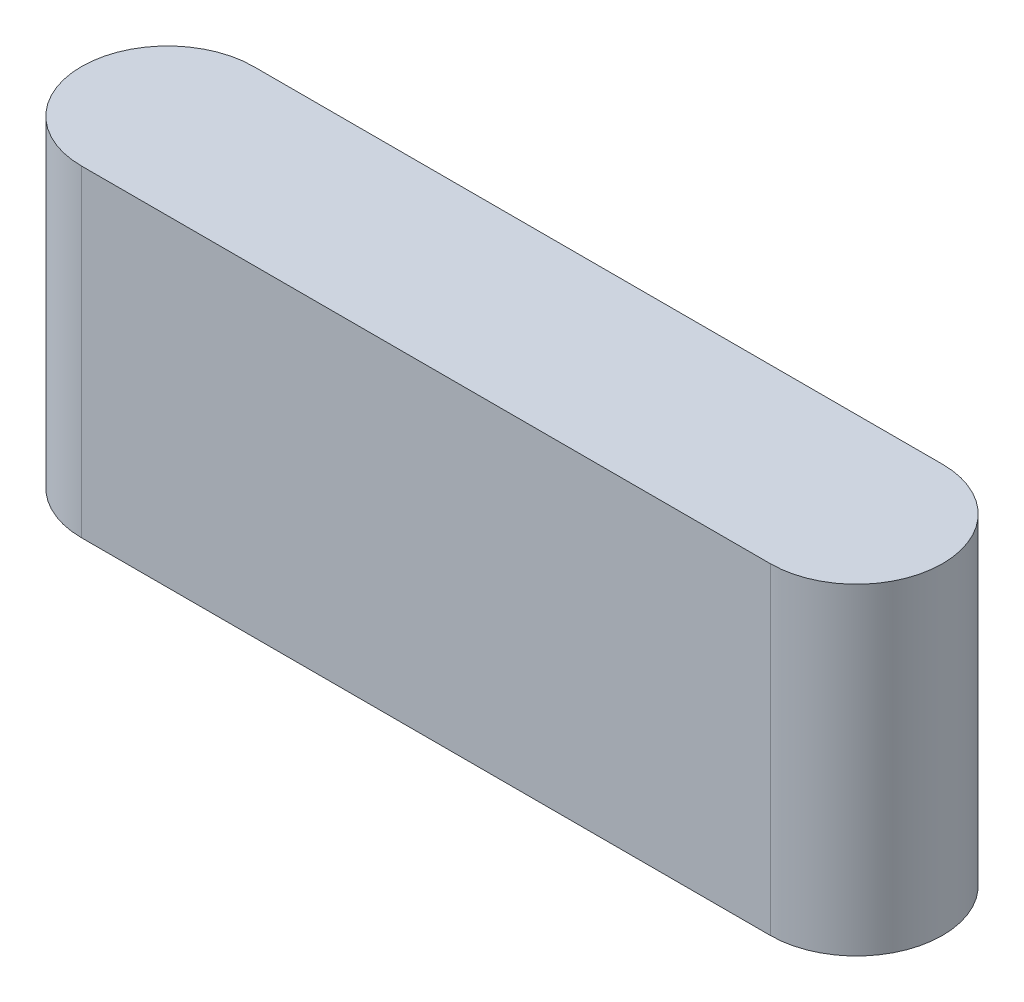
SolidWorks part; units mm, degrees
ref_plane "Front Plane" through (0, 0, 0) normal (0, 0, 1) x (1, 0, 0)
ref_plane "Top Plane" through (0, 0, 0) normal (0, 1, 0) x (1, 0, 0)
ref_plane "Right Plane" through (0, 0, 0) normal (1, 0, 0) x (0, 0, -1)
sketch "Sketch1" plane through (0, 0, 0) normal (0, 1, 0) x (1, 0, 0)
  line L0 (0, 0) -> (92, 0) construction
  line L1 (0, 11.5) -> (92, 11.5)
  line L2 (0, -11.5) -> (92, -11.5)
  arc A0 (0, 11.5) -> (0, -11.5) centre (0, 0) ccw
  arc A1 (92, -11.5) -> (92, 11.5) centre (92, 0) ccw
  point P3 (46, 0)
  dimension "D1" = 11.5
  dimension "D2" = 92
extrude "Boss-Extrude1" add sketch "Sketch1" along normal blind 43
